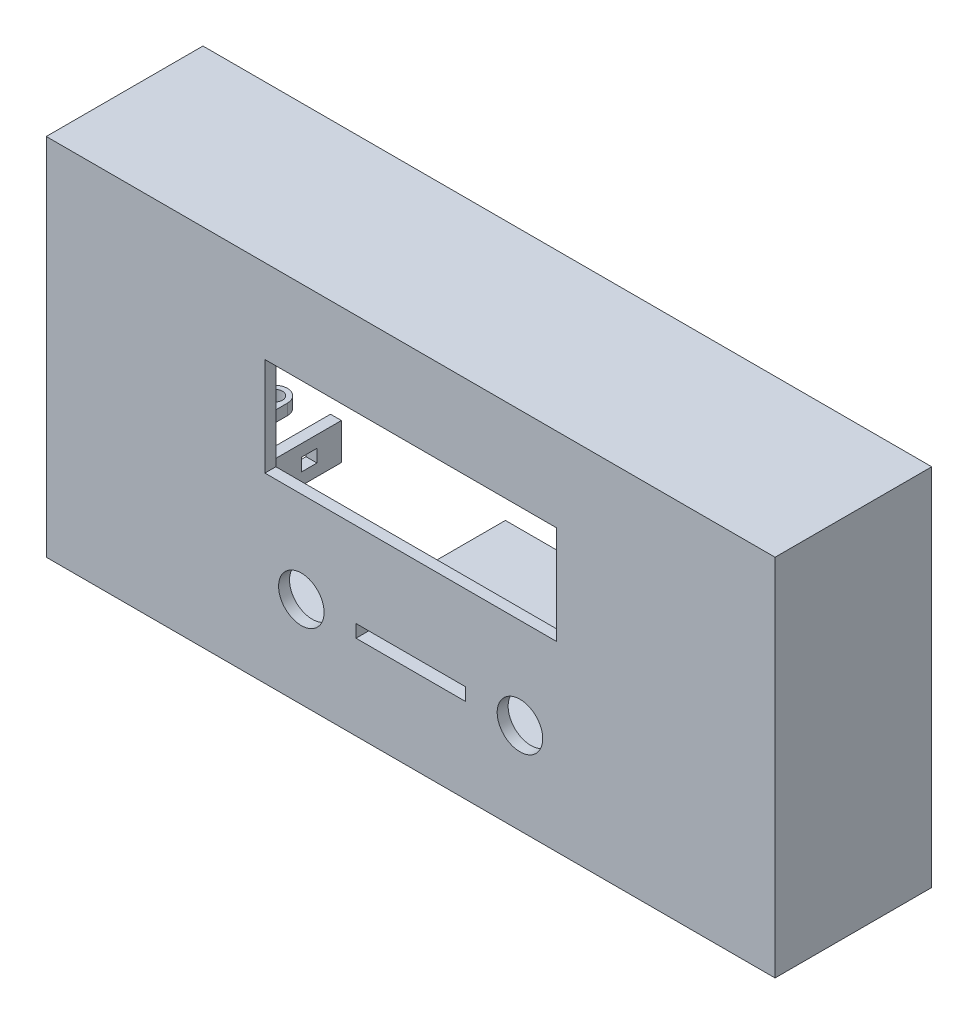
SolidWorks part; units mm, degrees
ref_plane "Спереди" through (0, 0, 0) normal (0, 0, 1) x (1, 0, 0)
ref_plane "Сверху" through (0, 0, 0) normal (0, 1, 0) x (1, 0, 0)
ref_plane "Справа" through (0, 0, 0) normal (1, 0, 0) x (0, 0, -1)
other "Configuration Table"
sketch "Эскиз1" plane through (0, 0, 0) normal (0, 0, 1) x (1, 0, 0)
  line L0 (0, 27) -> (-9.125, 27) construction
  line L1 (0, 0) -> (80, 0)
  line L2 (0, 0) -> (0, 27)
  line L3 (0, 27) -> (80, 27)
  line L4 (80, 0) -> (80, 27)
  line L5 (-9.125, -16.5) -> (89.125, -16.5) construction
  line L6 (-9.125, -16.5) -> (-9.125, 43.5) construction
  line L7 (-9.125, 43.5) -> (89.125, 43.5) construction
  line L8 (89.125, -16.5) -> (89.125, 43.5) construction
  line L9 (80, 27) -> (89.125, 27) construction
  line L10 (0, 27) -> (0, 43.5) construction
  line L11 (0, 0) -> (0, -16.5) construction
  line L12 (40, -25) -> (40, 0) construction
  line L13 (-60, 50) -> (140, 50)
  line L14 (-60, 50) -> (-60, -50)
  line L15 (25, -26.75) -> (55, -26.75)
  line L16 (25, -26.75) -> (25, -23.25)
  line L17 (25, -23.25) -> (55, -23.25)
  line L18 (55, -26.75) -> (55, -23.25)
  line L19 (25, -26.75) -> (55, -23.25) construction
  line L20 (25, -23.25) -> (55, -26.75) construction
  line L21 (-60, -50) -> (140, -50)
  line L22 (140, 50) -> (140, -50)
  line L23 (40, -25) -> (-60, -25) construction
  line L24 (40, -25) -> (140, -25) construction
  line L25 (70, -25) -> (10, -25) construction
  circle A0 centre (10, -25) radius 6.25
  circle A1 centre (70, -25) radius 6.25
  point P16 (40, -25)
  point P19 (40, -25)
  point P30 (40, -25)
  dimension "D8" = 100
  dimension "D12" = 12.5
  dimension "D1" = 80
  dimension "D2" = 27
  dimension "D3" = 98.25
  dimension "D4" = 60
  dimension "D5" = 25
  dimension "D6" = 3.5
  dimension "D7" = 30
  dimension "D9" = 25
  dimension "D10" = 75
  dimension "D11" = 30
extrude "Бобышка-Вытянуть1" add sketch "Эскиз1" along normal blind 3
sketch "Эскиз2" plane through (0, 0, 0) normal (0, 0, -1) x (-1, 0, 0)
  line L0 (-89.125, 43.5) -> (-86.625, 43.5) construction
  line L1 (9.125, 43.5) -> (-89.125, 43.5) construction
  line L2 (-86.625, 43.5) -> (-86.625, 41) construction
  line L3 (-40, -25) -> (-40, 0) construction
  line L4 (0, 0) -> (-80, 0) construction
  line L5 (-80, 13.5) -> (0, 13.5) construction
  line L6 (-80, 0) -> (-80, 27) construction
  line L7 (0, 0) -> (0, 27) construction
  circle A0 centre (-86.625, 41) radius 1.5
  circle A1 centre (-86.625, -14) radius 1.5
  circle A2 centre (6.625, 41) radius 1.5
  circle A3 centre (6.625, -14) radius 1.5
  circle A4 centre (-86.625, 41) radius 3
  circle A5 centre (-86.625, -14) radius 3
  circle A6 centre (6.625, -14) radius 3
  circle A7 centre (6.625, 41) radius 3
  dimension "D1" = 2.5
  dimension "D3" = 3
  dimension "D4" = 6
  dimension "D2" = 2.5
extrude "Бобышка-Вытянуть2" add sketch "Эскиз2" along normal blind 9
sketch "Эскиз4" plane through (0, 0, 0) normal (0, 0, -1) x (-1, 0, 0)
  line L1 (-55, -26.75) -> (-25, -26.75)
  line L2 (-55, -26.75) -> (-55, -23.25)
  line L3 (-55, -23.25) -> (-25, -23.25)
  line L4 (-25, -26.75) -> (-25, -23.25)
  line L5 (-57, -28.75) -> (-23, -28.75)
  line L6 (-57, -28.75) -> (-57, -21.25)
  line L7 (-57, -21.25) -> (-23, -21.25)
  line L8 (-23, -28.75) -> (-23, -21.25)
  line L9 (-140, 50) -> (60, 50)
  line L10 (-140, 50) -> (-140, -50)
  line L11 (-140, -50) -> (60, -50)
  line L12 (60, 50) -> (60, -50)
  line L13 (-137, 47) -> (57, 47)
  line L14 (-137, 47) -> (-137, -47)
  line L15 (-137, -47) -> (57, -47)
  line L16 (57, 47) -> (57, -47)
  dimension "D1" = 2
  dimension "D5" = 3
  dimension "D6" = 3
  dimension "D2" = 2
  dimension "D3" = 2
  dimension "D4" = 2
  dimension "D7" = 3
  dimension "D8" = 3
extrude "Бобышка-Вытянуть3" add sketch "Эскиз4" along normal blind 40
sketch "Эскиз5" plane through (23, 0, 0) normal (-1, 0, 0) x (0, 0, 1)
  line L1 (3, -23.25) -> (-40, -23.25) construction
  line L2 (-38, -26.75) -> (-24, -26.75)
  line L3 (-38, -26.75) -> (-38, -23.25)
  line L4 (-38, -23.25) -> (-24, -23.25)
  line L5 (-24, -26.75) -> (-24, -23.25)
  line L6 (3, -26.75) -> (-40, -26.75) construction
  line L7 (-40, -28.75) -> (-40, -21.25) construction
  dimension "D1" = 0
  dimension "D2" = 0
  dimension "D3" = 14
  dimension "D4" = 2
extrude "Вырез-Вытянуть1" cut sketch "Эскиз5" against normal blind 3
sketch "Эскиз6" plane through (0, 0, 0) normal (0, 0, -1) x (-1, 0, 0)
  line L0 (-23, -28.75) -> (-23, -21.25) construction
  line L1 (22, -20) -> (25, -20)
  line L2 (22, -20) -> (22, -30)
  line L3 (22, -30) -> (25, -30)
  line L4 (25, -20) -> (25, -30)
  line L5 (24.0409, -30) -> (24.0409, -26.5) construction
  line L6 (-18.7421, -26.5) -> (29.9351, -26.5) construction
  line L7 (24.4175, -20) -> (24.4175, -23.5) construction
  line L8 (-18.7421, -23.5) -> (29.9351, -23.5) construction
  dimension "D1" = 3
  dimension "D2" = 45
  dimension "D3" = 10
extrude "Бобышка-Вытянуть4" add sketch "Эскиз6" along normal up to surface (40 mm away) up to face at (40, -25, -40)
sketch "Эскиз7" plane through (-25, 0, 0) normal (-1, 0, 0) x (0, 0, 1)
  line L0 (-33.0404, -23.5) -> (-30.0404, -23.5) construction
  line L1 (-33.2904, -26.75) -> (-29.0404, -26.75)
  line L2 (-33.2904, -26.75) -> (-33.2904, -23.25)
  line L3 (-33.2904, -23.25) -> (-29.0404, -23.25)
  line L4 (-29.0404, -26.75) -> (-29.0404, -23.25)
  line L5 (-33.0404, -23.5) -> (-33.0404, -26.5) construction
  line L6 (-30.0404, -23.5) -> (-30.0404, -26.5) construction
  line L7 (-33.0404, -26.5) -> (-30.0404, -26.5) construction
  dimension "D1" = 0.25
  dimension "D2" = 0.25
  dimension "D3" = 1
  dimension "D4" = 0.25
extrude "Вырез-Вытянуть2" cut sketch "Эскиз7" against normal blind 5
sketch "Эскиз9" plane through (0, -26.75, 0) normal (0, 1, 0) x (1, 0, 0)
  line L0 (-31.5383, 34.7393) -> (-31.5383, 0)
  line L1 (137, 0) -> (-57, 0) construction
  line L2 (-31.5383, 0) -> (-57, 0)
  line L3 (-57, 0) -> (-57, 34.7393)
  line L4 (-57, 40) -> (-57, 0) construction
  line L5 (-57, 38.2393) -> (-35.0383, 38.2393) construction
  line L6 (-38.5383, 34.7393) -> (-57, 34.7393)
  line L7 (-57, 34.7393) -> (-57, 38.2393) construction
  arc A0 (-31.5383, 34.7393) -> (-35.0383, 38.2393) centre (-35.0383, 34.7393) ccw
  arc A1 (-31.8588, 33.2762) -> (-38.2179, 36.2024) centre (-35.0383, 34.7393) ccw construction
  circle A2 centre (-49.5622, 3.1758) radius 2.125
  circle A3 centre (-35.0383, 34.7393) radius 2.125
  circle A4 centre (-49, 22.0404) radius 4.75
  arc A5 (-35.0383, 38.2393) -> (-38.5383, 34.7393) centre (-35.0383, 34.7393) ccw
  dimension "D1" = 0
  dimension "D2" = 9.5
extrude "Бобышка-Вытянуть5" add sketch "Эскиз9" along normal blind 2 and the other way blind 1 from surface at 6.75 starting at face at (-23.5, -20, -20)
sketch "Эскиз10" plane through (0, 0, 0) normal (0, 0, -1) x (-1, 0, 0)
  circle A0 centre (23, 40) radius 1.5
  circle A1 centre (50, 40) radius 1.5
  circle A2 centre (23, 10) radius 1.5
  circle A3 centre (50, 10) radius 1.5
  circle A4 centre (50, 10) radius 3
  circle A5 centre (23, 10) radius 3
  circle A6 centre (23, 40) radius 3
  circle A7 centre (50, 40) radius 3
extrude "Бобышка-Вытянуть6" add sketch "Эскиз10" along normal blind 5
sketch "Эскиз11" plane through (0, 0, 0) normal (0, 0, -1) x (-1, 0, 0)
  circle A0 centre (-120.5, 35.5) radius 0.5
  circle A1 centre (-120.5, 35.5) radius 1.5
  circle A2 centre (-105.15, 35.5) radius 1.5
  circle A3 centre (-105.15, 35.5) radius 0.5
  circle A4 centre (-105.15, -5.5) radius 0.5
  circle A5 centre (-105.15, -5.5) radius 1.5
  circle A6 centre (-120.5, -5.5) radius 0.5
  circle A7 centre (-120.5, -5.5) radius 1.5
extrude "Бобышка-Вытянуть7" add sketch "Эскиз11" along normal blind 5
sketch "Эскиз12" plane through (0, 0, -40) normal (0, 0, -1) x (-1, 0, 0)
  line L0 (-140, 50) -> (-140, -50) construction
  line L1 (-140, 50) -> (60, 50) construction
  line L2 (-140, 40) -> (-140, 50)
  line L3 (-140, 50) -> (-130, 50)
  line L4 (-40, 50) -> (-40, -50) construction
  line L5 (-140, -50) -> (60, -50) construction
  line L6 (-140, 0) -> (60, 0) construction
  line L7 (60, 50) -> (60, -50) construction
  line L8 (60, 40) -> (60, 50)
  line L9 (60, 50) -> (50, 50)
  line L10 (60, -50) -> (50, -50)
  line L11 (60, -40) -> (60, -50)
  line L12 (-140, -50) -> (-130, -50)
  line L13 (-140, -40) -> (-140, -50)
  arc A0 (-140, 40) -> (-130, 50) centre (-140, 50) ccw
  arc A1 (60, 40) -> (50, 50) centre (60, 50) cw
  arc A2 (60, -40) -> (50, -50) centre (60, -50) ccw
  arc A3 (-140, -40) -> (-130, -50) centre (-140, -50) cw
  dimension "D1" = 10
extrude "Бобышка-Вытянуть8" add sketch "Эскиз12" against normal blind 1 from offset 3 offset against normal yes
fillet "Скругление1" radius 2 8 edges at (-53.7303, -47, -36) (-57, -43.7303, -36) (137, -43.7303, -36) (133.7303, -47, -36) (133.7303, 47, -36) (137, 43.7303, -36) (-53.7303, 47, -36) (-57, 43.7303, -36)
